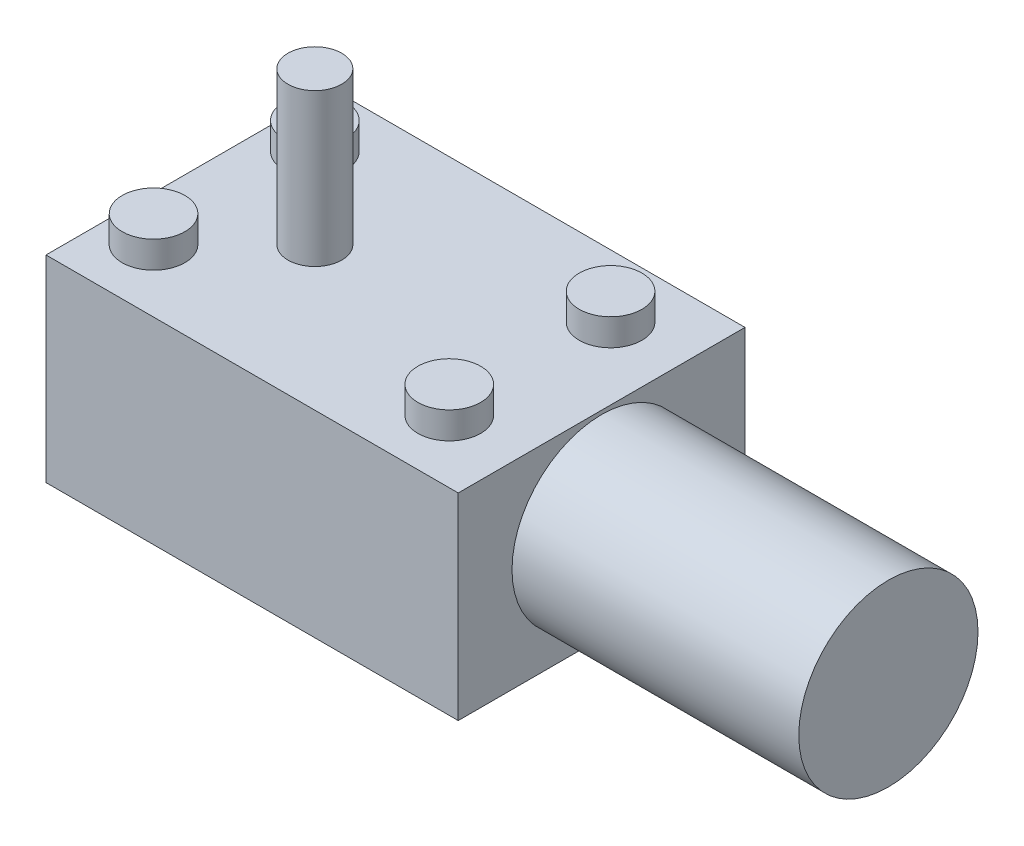
SolidWorks part; units mm, degrees
ref_plane "Front Plane" through (0, 0, 0) normal (0, 0, 1) x (1, 0, 0)
ref_plane "Top Plane" through (0, 0, 0) normal (0, 1, 0) x (1, 0, 0)
ref_plane "Right Plane" through (0, 0, 0) normal (1, 0, 0) x (0, 0, -1)
sketch "Sketch1" plane through (0, 0, 0) normal (0, 1, 0) x (1, 0, 0)
  line L1 (-23, 16) -> (23, 16)
  line L2 (-23, 16) -> (-23, -16)
  line L3 (-23, -16) -> (23, -16)
  line L4 (23, 16) -> (23, -16)
  line L5 (-23, 16) -> (23, -16) construction
  line L6 (-23, -16) -> (23, 16) construction
  point P0 (0, 0)
  dimension "D1" = 46
  dimension "D2" = 32
extrude "Boss-Extrude1" add sketch "Sketch1" along normal blind 22
sketch "Sketch3" plane through (23, 0, 0) normal (1, 0, 0) x (0, 0, -1)
  circle A0 centre (0, 11.5777) radius 10
extrude "Boss-Extrude3" add sketch "Sketch3" along normal blind 32
sketch "Sketch4" plane through (0, 22, 0) normal (0, 1, 0) x (1, 0, 0)
  line L0 (-23, 0) -> (23, 0) construction
  line L1 (-23, 16) -> (-23, -16) construction
  line L2 (23, -16) -> (23, 16) construction
  line L3 (-23, 0) -> (-9, 0)
  circle A0 centre (-9, 0) radius 3
extrude "Boss-Extrude4" add sketch "Sketch4" along normal blind 17 contours L3 L0 A0 | L0 L3 A0
sketch "Sketch5" plane through (0, 22, 0) normal (0, 1, 0) x (1, 0, 0)
  line L0 (-23, 0) -> (23, 0) construction
  line L1 (-23, 16) -> (-23, -16) construction
  line L2 (23, -10) -> (23, 10) construction
  line L4 (-23, 0) -> (-18, 0)
  line L5 (-23, 0) -> (-23, 9)
  line L6 (-23, 9) -> (-18, 9)
  line L7 (-18, 0) -> (-18, 9)
  circle A0 centre (-18, 9) radius 3.5
  circle A1 centre (-18, -9) radius 3.5
  circle A2 centre (15, -9) radius 3.5
  circle A3 centre (15, 9) radius 3.5
  dimension "D3" = 2
  dimension "D1" = 9
  dimension "D2" = 5
extrude "Boss-Extrude6" add sketch "Sketch5" along normal blind 3 contours A1 | A3 | A2 | A0
